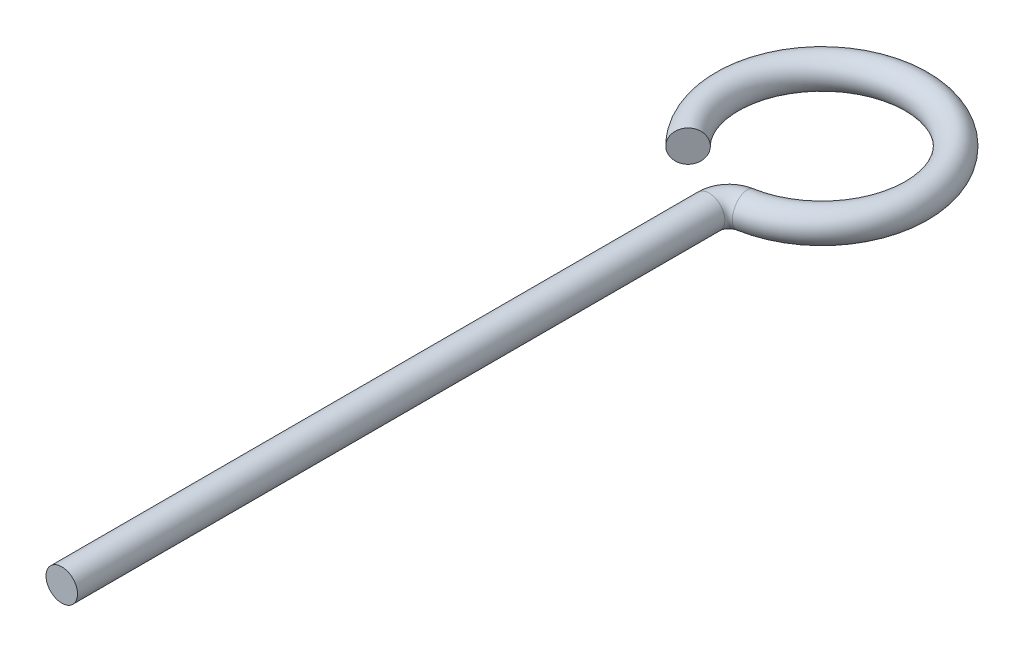
SolidWorks part; units mm, degrees
ref_plane "Plano frontal" through (0, 0, 0) normal (0, 0, 1) x (1, 0, 0)
ref_plane "Plano superior" through (0, 0, 0) normal (0, 1, 0) x (1, 0, 0)
ref_plane "Plano direito" through (0, 0, 0) normal (1, 0, 0) x (0, 0, -1)
sketch "Esboço1" plane through (0, 0, 0) normal (0, 1, 0) x (1, 0, 0)
  line L0 (0, 0) -> (0, 65.0551)
  line L1 (0, 66.88) -> (0, 85.9) construction
  arc A1 (1.6525, 67.0247) -> (-6.7246, 69.6654) centre (0, 76.39) ccw
  arc A2 (0, 65.0551) -> (1.6525, 67.0247) centre (2, 65.0551) cw
  dimension "D1" = 85.9
  dimension "D2" = 9.51
  dimension "D3" = 2
sketch "Esboço2" plane through (0, 0, 0) normal (0, 0, 1) x (1, 0, 0)
  circle A0 centre (0, 0) radius 1.585
  dimension "D1" = 3.17
sweep "Varredura1" add profiles "Esboço2" path "Esboço1"
